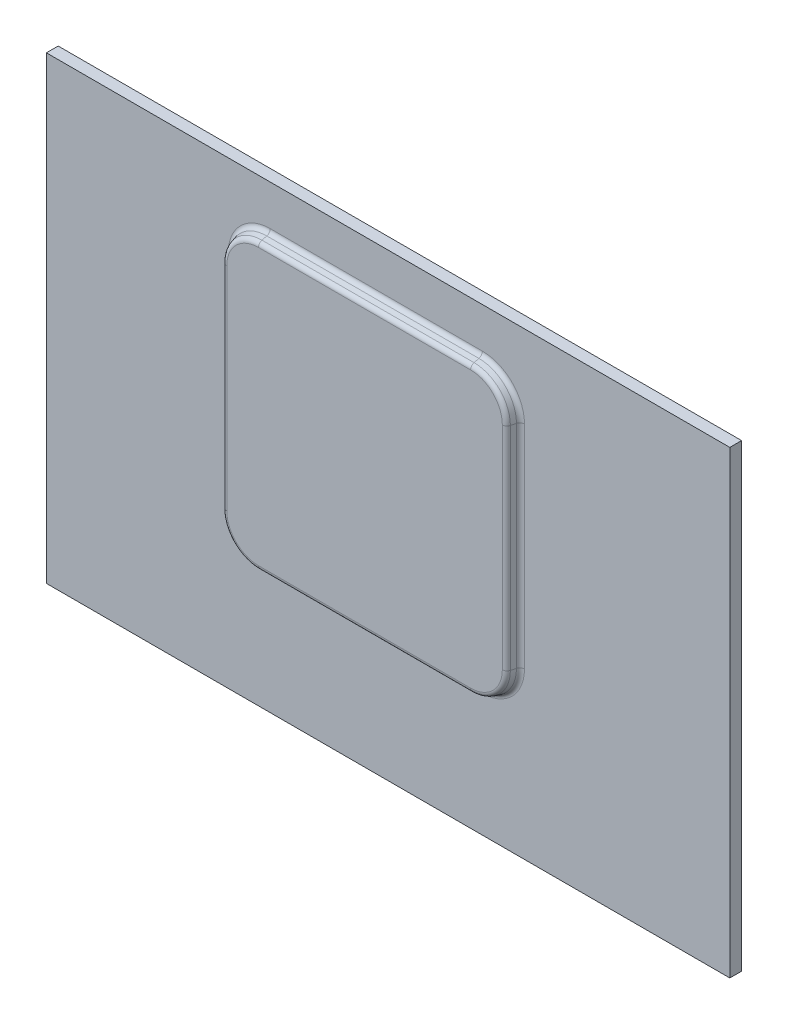
SolidWorks part; units mm, degrees
ref_plane "前视基准面" through (0, 0, 0) normal (0, 0, 1) x (1, 0, 0)
ref_plane "上视基准面" through (0, 0, 0) normal (0, 1, 0) x (1, 0, 0)
ref_plane "右视基准面" through (0, 0, 0) normal (1, 0, 0) x (0, 0, -1)
sketch "草图1" plane through (0, 0, 0) normal (0, 0, 1) x (1, 0, 0)
  line L1 (145, -97.5) -> (-145, -97.5)
  line L2 (145, -97.5) -> (145, 97.5)
  line L3 (145, 97.5) -> (-145, 97.5)
  line L4 (-145, -97.5) -> (-145, 97.5)
  line L5 (145, -97.5) -> (-145, 97.5) construction
  line L6 (145, 97.5) -> (-145, -97.5) construction
  point P0 (0, 0)
  dimension "D1" = 290
  dimension "D2" = 195
extrude "凸台-拉伸1" add sketch "草图1" along normal blind 5
sketch "草图2" plane through (0, 0, 5) normal (0, 0, 1) x (1, 0, 0)
  line L0 (145, 97.5) -> (-145, 97.5) construction
  line L1 (55, 77.5) -> (-65, 77.5)
  line L2 (55, 77.5) -> (55, -42.5)
  line L3 (55, -42.5) -> (-65, -42.5)
  line L4 (-65, 77.5) -> (-65, -42.5)
  line L5 (55, 77.5) -> (-65, -42.5) construction
  line L6 (55, -42.5) -> (-65, 77.5) construction
  line L7 (-145, 97.5) -> (-145, -97.5) construction
  point P0 (-5, 17.5)
  dimension "D1" = 120
  dimension "D2" = 120
  dimension "D3" = 20
  dimension "D4" = 80
extrude "凸台-拉伸2" add sketch "草图2" along normal blind 5
fillet "圆角1" radius 15 4 edges at (-65, -42.5, 7.5) (55, -42.5, 7.5) (-65, 77.5, 7.5) (55, 77.5, 7.5)
draft "拔模1" type of draft neutral plane draft angle 15 faces to draft 8 face at (-65, 17.5, 7.5) face at (-59.0533, 71.5533, 7.5) face at (-5, 77.5, 7.5) face at (49.0533, 71.5533, 7.5) face at (55, 17.5, 7.5) face at (49.0533, -36.5533, 7.5) face at (-5, -42.5, 7.5) face at (-59.0533, -36.5533, 7.5) neutral plane through (0, 0, 10) neutral plane normal (0, 0, 1) parameters "D1"=15
fillet "圆角2" radius 2 16 edges at (-61.5539, -39.0539, 5) (-66.3397, 17.5, 5) (-61.5539, 74.0539, 5) (-5, 78.8397, 5) (51.5539, 74.0539, 5) (56.3397, 17.5, 5) (51.5539, -39.0539, 5) (-60.6066, -38.1066, 10) (-65, 17.5, 10) (-60.6066, 73.1066, 10) (-5, 77.5, 10) (50.6066, 73.1066, 10) (55, 17.5, 10) (50.6066, -38.1066, 10) (-5, -43.8397, 5) (-5, -42.5, 10)
sketch "方向草图" plane through (0, 0, 5) normal (0, 0, 1) x (1, 0, 0)
  line L0 (40, -45.3744) -> (-50, -45.3744) construction
  line L1 (-67.8744, -27.5) -> (-67.8744, 62.5) construction
  line L2 (-50, 80.3744) -> (40, 80.3744) construction
  line L3 (57.8744, 62.5) -> (57.8744, -27.5) construction
  line L4 (-145, 97.5) -> (-145, -97.5) construction
  line L5 (-145, -97.5) -> (145, -97.5) construction
  line L6 (145, -97.5) -> (145, 97.5) construction
  line L7 (145, 97.5) -> (-145, 97.5) construction
  line L8 (40, -45.3744) -> (-50, -45.3744)
  line L9 (-67.8744, -27.5) -> (-67.8744, 62.5)
  line L10 (-50, 80.3744) -> (40, 80.3744)
  line L11 (57.8744, 62.5) -> (57.8744, -27.5)
  line L12 (-145, 97.5) -> (-145, -97.5) construction
  line L13 (-145, -97.5) -> (145, -97.5) construction
  line L14 (145, -97.5) -> (145, 97.5) construction
  line L15 (145, 97.5) -> (-145, 97.5) construction
  arc A0 (-67.8744, -27.5) -> (-50, -45.3744) centre (-50, -27.5) ccw construction
  arc A1 (-50, 80.3744) -> (-67.8744, 62.5) centre (-50, 62.5) ccw construction
  arc A2 (57.8744, 62.5) -> (40, 80.3744) centre (40, 62.5) ccw construction
  arc A3 (40, -45.3744) -> (57.8744, -27.5) centre (40, -27.5) ccw construction
  arc A4 (-67.8744, -27.5) -> (-50, -45.3744) centre (-50, -27.5) ccw
  arc A5 (-50, 80.3744) -> (-67.8744, 62.5) centre (-50, 62.5) ccw
  arc A6 (57.8744, 62.5) -> (40, 80.3744) centre (40, 62.5) ccw
  arc A7 (40, -45.3744) -> (57.8744, -27.5) centre (40, -27.5) ccw
  point P14 (0, 0)
other "成形工具1"
